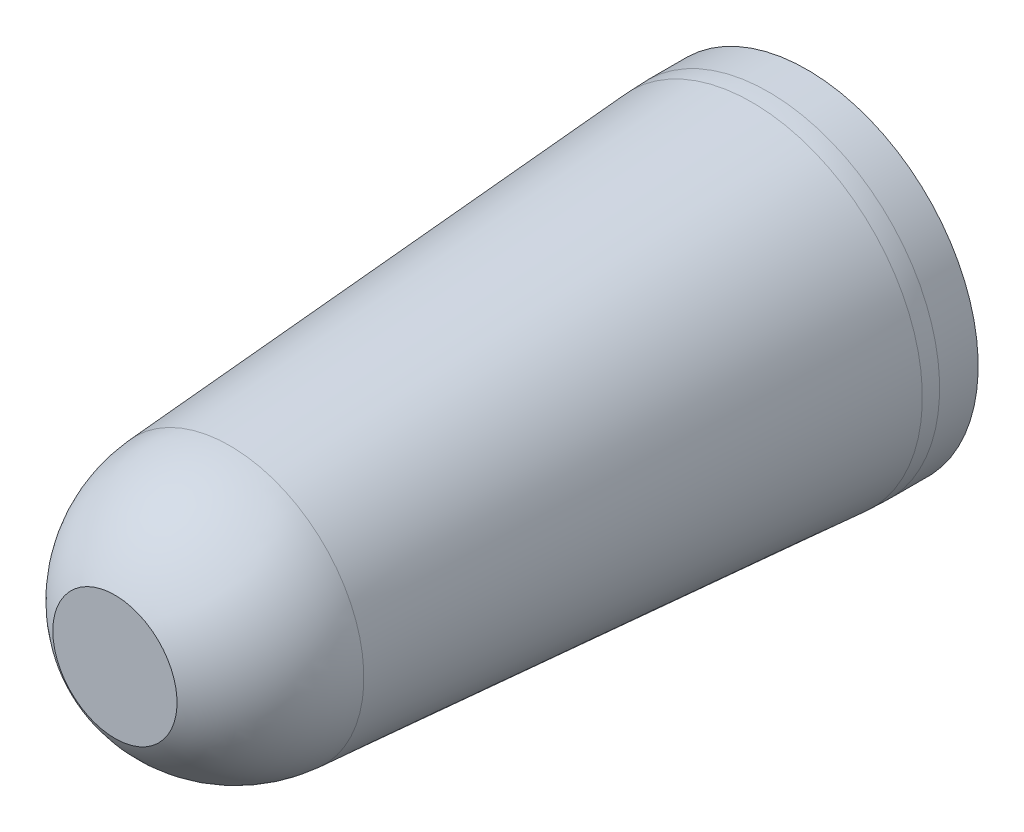
SolidWorks part; units mm, degrees
ref_plane "Front Plane" through (0, 0, 0) normal (0, 0, 1) x (1, 0, 0)
ref_plane "Top Plane" through (0, 0, 0) normal (0, 1, 0) x (1, 0, 0)
ref_plane "Right Plane" through (0, 0, 0) normal (1, 0, 0) x (0, 0, -1)
sketch "Sketch1" plane through (0, 0, 0) normal (1, 0, 0) x (0, 0, -1)
  line L2 (0, 49.7479) -> (-12.8781, 49.7479)
  line L3 (-192.8546, 37.3578) -> (-18.4523, 49.5532)
  line L4 (0, 49.7479) -> (0, -7.4021)
  line L5 (0, -7.4021) -> (-231.2742, -7.4021)
  line L6 (-231.2742, -7.4021) -> (-231.2742, 13.3506)
  arc A2 (-12.8781, 49.7479) -> (-18.4523, 49.5532) centre (-12.8781, -30.1621) ccw
  arc A3 (-192.8546, 37.3578) -> (-231.2742, 13.3506) centre (-189.4889, -10.7742) ccw
  dimension "D1" = 57.15
revolve "Revolve1" add sketch "Sketch1" angle 360 about L5
